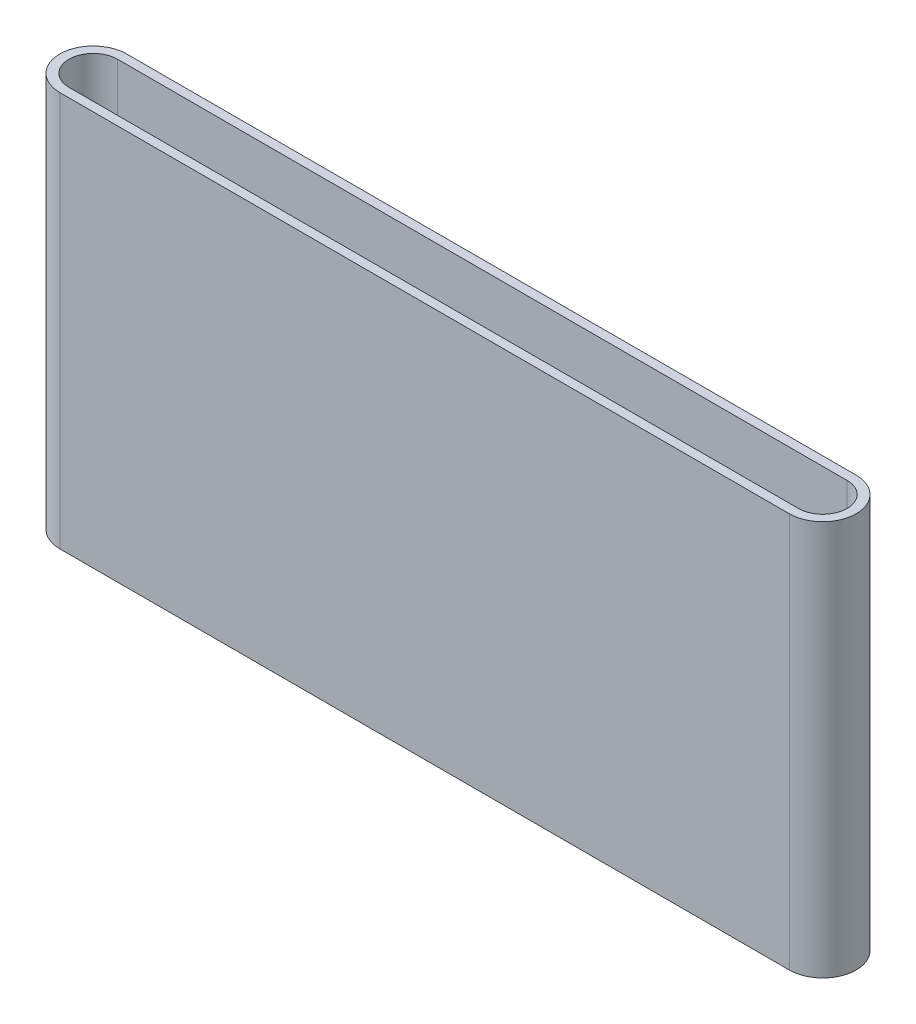
SolidWorks part; units mm, degrees
ref_plane "Front Plane" through (0, 0, 0) normal (0, 0, 1) x (1, 0, 0)
ref_plane "Top Plane" through (0, 0, 0) normal (0, 1, 0) x (1, 0, 0)
ref_plane "Right Plane" through (0, 0, 0) normal (1, 0, 0) x (0, 0, -1)
sketch "Sketch1" plane through (0, 0, 0) normal (0, 1, 0) x (1, 0, 0)
  line L0 (0, 0) -> (120, 0) construction
  line L1 (0, 4) -> (120, 4)
  line L2 (0, -4) -> (120, -4)
  line L3 (0, 5.5) -> (120, 5.5)
  line L4 (0, -5.5) -> (120, -5.5)
  arc A0 (0, 4) -> (0, -4) centre (0, 0) ccw
  arc A1 (120, -4) -> (120, 4) centre (120, 0) ccw
  arc A2 (120, -5.5) -> (120, 5.5) centre (120, 0) ccw
  arc A3 (0, 5.5) -> (0, -5.5) centre (0, 0) ccw
  dimension "D1" = 8
  dimension "D3" = 8
  dimension "D2" = 120
  dimension "D4" = 1.5
extrude "Boss-Extrude1" add sketch "Sketch1" along normal blind 65
